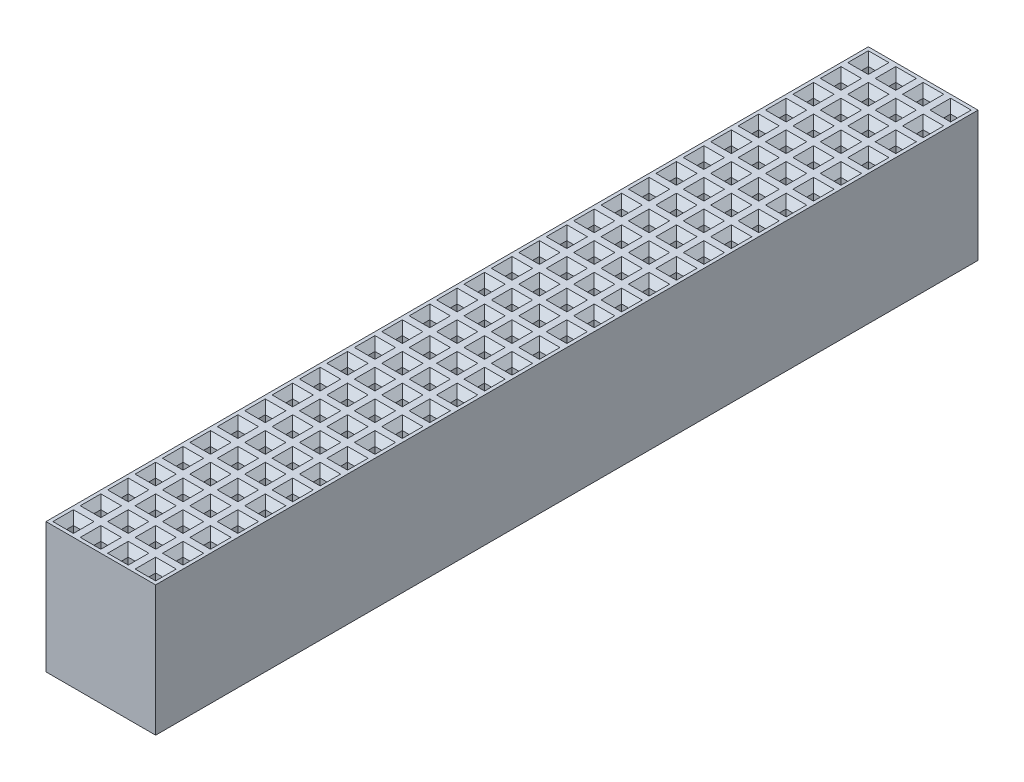
SolidWorks part; units mm, degrees
ref_plane "Alzado" through (0, 0, 0) normal (0, 0, 1) x (1, 0, 0)
ref_plane "Planta" through (0, 0, 0) normal (0, 1, 0) x (1, 0, 0)
ref_plane "Vista lateral" through (0, 0, 0) normal (1, 0, 0) x (0, 0, -1)
sketch "Croquis1" plane through (0, 0, 0) normal (0, 1, 0) x (1, 0, 0)
  line L1 (0, 0) -> (8, 0)
  line L2 (0, 0) -> (0, 60)
  line L3 (0, 60) -> (8, 60)
  line L4 (8, 0) -> (8, 60)
  dimension "D1" = 60
  dimension "D2" = 8
extrude "Extruir1" add sketch "Croquis1" along normal blind 9.5
sketch "Croquis2" plane through (0, 9.5, 0) normal (0, 1, 0) x (1, 0, 0)
  line L0 (0, 0) -> (8, 0) construction
  line L1 (6.75, 1.25) -> (7.25, 1.25)
  line L2 (6.75, 1.25) -> (6.75, 0.75)
  line L3 (6.75, 0.75) -> (7.25, 0.75)
  line L4 (7.25, 1.25) -> (7.25, 0.75)
  line L5 (8, 0) -> (8, 60) construction
  line L6 (4.75, 1.25) -> (5.25, 1.25)
  line L7 (4.75, 1.25) -> (4.75, 0.75)
  line L8 (4.75, 0.75) -> (5.25, 0.75)
  line L9 (5.25, 1.25) -> (5.25, 0.75)
  line L10 (2.75, 1.25) -> (3.25, 1.25)
  line L11 (2.75, 1.25) -> (2.75, 0.75)
  line L12 (2.75, 0.75) -> (3.25, 0.75)
  line L13 (3.25, 1.25) -> (3.25, 0.75)
  line L14 (0.75, 1.25) -> (1.25, 1.25)
  line L15 (0.75, 1.25) -> (0.75, 0.75)
  line L16 (0.75, 0.75) -> (1.25, 0.75)
  line L17 (1.25, 1.25) -> (1.25, 0.75)
  line L18 (6.75, 3.25) -> (7.25, 3.25)
  line L19 (6.75, 3.25) -> (6.75, 2.75)
  line L20 (6.75, 2.75) -> (7.25, 2.75)
  line L21 (7.25, 3.25) -> (7.25, 2.75)
  line L22 (4.75, 3.25) -> (5.25, 3.25)
  line L23 (4.75, 3.25) -> (4.75, 2.75)
  line L24 (4.75, 2.75) -> (5.25, 2.75)
  line L25 (5.25, 3.25) -> (5.25, 2.75)
  line L26 (2.75, 3.25) -> (3.25, 3.25)
  line L27 (2.75, 3.25) -> (2.75, 2.75)
  line L28 (2.75, 2.75) -> (3.25, 2.75)
  line L29 (3.25, 3.25) -> (3.25, 2.75)
  line L30 (0.75, 3.25) -> (1.25, 3.25)
  line L31 (0.75, 3.25) -> (0.75, 2.75)
  line L32 (0.75, 2.75) -> (1.25, 2.75)
  line L33 (1.25, 3.25) -> (1.25, 2.75)
  line L34 (6.75, 5.25) -> (7.25, 5.25)
  line L35 (6.75, 5.25) -> (6.75, 4.75)
  line L36 (6.75, 4.75) -> (7.25, 4.75)
  line L37 (7.25, 5.25) -> (7.25, 4.75)
  line L38 (4.75, 5.25) -> (5.25, 5.25)
  line L39 (4.75, 5.25) -> (4.75, 4.75)
  line L40 (4.75, 4.75) -> (5.25, 4.75)
  line L41 (5.25, 5.25) -> (5.25, 4.75)
  line L42 (2.75, 5.25) -> (3.25, 5.25)
  line L43 (2.75, 5.25) -> (2.75, 4.75)
  line L44 (2.75, 4.75) -> (3.25, 4.75)
  line L45 (3.25, 5.25) -> (3.25, 4.75)
  line L46 (0.75, 5.25) -> (1.25, 5.25)
  line L47 (0.75, 5.25) -> (0.75, 4.75)
  line L48 (0.75, 4.75) -> (1.25, 4.75)
  line L49 (1.25, 5.25) -> (1.25, 4.75)
  line L50 (6.75, 7.25) -> (7.25, 7.25)
  line L51 (6.75, 7.25) -> (6.75, 6.75)
  line L52 (6.75, 6.75) -> (7.25, 6.75)
  line L53 (7.25, 7.25) -> (7.25, 6.75)
  line L54 (4.75, 7.25) -> (5.25, 7.25)
  line L55 (4.75, 7.25) -> (4.75, 6.75)
  line L56 (4.75, 6.75) -> (5.25, 6.75)
  line L57 (5.25, 7.25) -> (5.25, 6.75)
  line L58 (2.75, 7.25) -> (3.25, 7.25)
  line L59 (2.75, 7.25) -> (2.75, 6.75)
  line L60 (2.75, 6.75) -> (3.25, 6.75)
  line L61 (3.25, 7.25) -> (3.25, 6.75)
  line L62 (0.75, 7.25) -> (1.25, 7.25)
  line L63 (0.75, 7.25) -> (0.75, 6.75)
  line L64 (0.75, 6.75) -> (1.25, 6.75)
  line L65 (1.25, 7.25) -> (1.25, 6.75)
  line L66 (6.75, 9.25) -> (7.25, 9.25)
  line L67 (6.75, 9.25) -> (6.75, 8.75)
  line L68 (6.75, 8.75) -> (7.25, 8.75)
  line L69 (7.25, 9.25) -> (7.25, 8.75)
  line L70 (4.75, 9.25) -> (5.25, 9.25)
  line L71 (4.75, 9.25) -> (4.75, 8.75)
  line L72 (4.75, 8.75) -> (5.25, 8.75)
  line L73 (5.25, 9.25) -> (5.25, 8.75)
  line L74 (2.75, 9.25) -> (3.25, 9.25)
  line L75 (2.75, 9.25) -> (2.75, 8.75)
  line L76 (2.75, 8.75) -> (3.25, 8.75)
  line L77 (3.25, 9.25) -> (3.25, 8.75)
  line L78 (0.75, 9.25) -> (1.25, 9.25)
  line L79 (0.75, 9.25) -> (0.75, 8.75)
  line L80 (0.75, 8.75) -> (1.25, 8.75)
  line L81 (1.25, 9.25) -> (1.25, 8.75)
  line L82 (6.75, 11.25) -> (7.25, 11.25)
  line L83 (6.75, 11.25) -> (6.75, 10.75)
  line L84 (6.75, 10.75) -> (7.25, 10.75)
  line L85 (7.25, 11.25) -> (7.25, 10.75)
  line L86 (4.75, 11.25) -> (5.25, 11.25)
  line L87 (4.75, 11.25) -> (4.75, 10.75)
  line L88 (4.75, 10.75) -> (5.25, 10.75)
  line L89 (5.25, 11.25) -> (5.25, 10.75)
  line L90 (2.75, 11.25) -> (3.25, 11.25)
  line L91 (2.75, 11.25) -> (2.75, 10.75)
  line L92 (2.75, 10.75) -> (3.25, 10.75)
  line L93 (3.25, 11.25) -> (3.25, 10.75)
  line L94 (0.75, 11.25) -> (1.25, 11.25)
  line L95 (0.75, 11.25) -> (0.75, 10.75)
  line L96 (0.75, 10.75) -> (1.25, 10.75)
  line L97 (1.25, 11.25) -> (1.25, 10.75)
  line L98 (6.75, 13.25) -> (7.25, 13.25)
  line L99 (6.75, 13.25) -> (6.75, 12.75)
  line L100 (6.75, 12.75) -> (7.25, 12.75)
  line L101 (7.25, 13.25) -> (7.25, 12.75)
  line L102 (4.75, 13.25) -> (5.25, 13.25)
  line L103 (4.75, 13.25) -> (4.75, 12.75)
  line L104 (4.75, 12.75) -> (5.25, 12.75)
  line L105 (5.25, 13.25) -> (5.25, 12.75)
  line L106 (2.75, 13.25) -> (3.25, 13.25)
  line L107 (2.75, 13.25) -> (2.75, 12.75)
  line L108 (2.75, 12.75) -> (3.25, 12.75)
  line L109 (3.25, 13.25) -> (3.25, 12.75)
  line L110 (0.75, 13.25) -> (1.25, 13.25)
  line L111 (0.75, 13.25) -> (0.75, 12.75)
  line L112 (0.75, 12.75) -> (1.25, 12.75)
  line L113 (1.25, 13.25) -> (1.25, 12.75)
  line L114 (6.75, 15.25) -> (7.25, 15.25)
  line L115 (6.75, 15.25) -> (6.75, 14.75)
  line L116 (6.75, 14.75) -> (7.25, 14.75)
  line L117 (7.25, 15.25) -> (7.25, 14.75)
  line L118 (4.75, 15.25) -> (5.25, 15.25)
  line L119 (4.75, 15.25) -> (4.75, 14.75)
  line L120 (4.75, 14.75) -> (5.25, 14.75)
  line L121 (5.25, 15.25) -> (5.25, 14.75)
  line L122 (2.75, 15.25) -> (3.25, 15.25)
  line L123 (2.75, 15.25) -> (2.75, 14.75)
  line L124 (2.75, 14.75) -> (3.25, 14.75)
  line L125 (3.25, 15.25) -> (3.25, 14.75)
  line L126 (0.75, 15.25) -> (1.25, 15.25)
  line L127 (0.75, 15.25) -> (0.75, 14.75)
  line L128 (0.75, 14.75) -> (1.25, 14.75)
  line L129 (1.25, 15.25) -> (1.25, 14.75)
  line L130 (6.75, 17.25) -> (7.25, 17.25)
  line L131 (6.75, 17.25) -> (6.75, 16.75)
  line L132 (6.75, 16.75) -> (7.25, 16.75)
  line L133 (7.25, 17.25) -> (7.25, 16.75)
  line L134 (4.75, 17.25) -> (5.25, 17.25)
  line L135 (4.75, 17.25) -> (4.75, 16.75)
  line L136 (4.75, 16.75) -> (5.25, 16.75)
  line L137 (5.25, 17.25) -> (5.25, 16.75)
  line L138 (2.75, 17.25) -> (3.25, 17.25)
  line L139 (2.75, 17.25) -> (2.75, 16.75)
  line L140 (2.75, 16.75) -> (3.25, 16.75)
  line L141 (3.25, 17.25) -> (3.25, 16.75)
  line L142 (0.75, 17.25) -> (1.25, 17.25)
  line L143 (0.75, 17.25) -> (0.75, 16.75)
  line L144 (0.75, 16.75) -> (1.25, 16.75)
  line L145 (1.25, 17.25) -> (1.25, 16.75)
  line L146 (6.75, 19.25) -> (7.25, 19.25)
  line L147 (6.75, 19.25) -> (6.75, 18.75)
  line L148 (6.75, 18.75) -> (7.25, 18.75)
  line L149 (7.25, 19.25) -> (7.25, 18.75)
  line L150 (4.75, 19.25) -> (5.25, 19.25)
  line L151 (4.75, 19.25) -> (4.75, 18.75)
  line L152 (4.75, 18.75) -> (5.25, 18.75)
  line L153 (5.25, 19.25) -> (5.25, 18.75)
  line L154 (2.75, 19.25) -> (3.25, 19.25)
  line L155 (2.75, 19.25) -> (2.75, 18.75)
  line L156 (2.75, 18.75) -> (3.25, 18.75)
  line L157 (3.25, 19.25) -> (3.25, 18.75)
  line L158 (0.75, 19.25) -> (1.25, 19.25)
  line L159 (0.75, 19.25) -> (0.75, 18.75)
  line L160 (0.75, 18.75) -> (1.25, 18.75)
  line L161 (1.25, 19.25) -> (1.25, 18.75)
  line L162 (6.75, 21.25) -> (7.25, 21.25)
  line L163 (6.75, 21.25) -> (6.75, 20.75)
  line L164 (6.75, 20.75) -> (7.25, 20.75)
  line L165 (7.25, 21.25) -> (7.25, 20.75)
  line L166 (4.75, 21.25) -> (5.25, 21.25)
  line L167 (4.75, 21.25) -> (4.75, 20.75)
  line L168 (4.75, 20.75) -> (5.25, 20.75)
  line L169 (5.25, 21.25) -> (5.25, 20.75)
  line L170 (2.75, 21.25) -> (3.25, 21.25)
  line L171 (2.75, 21.25) -> (2.75, 20.75)
  line L172 (2.75, 20.75) -> (3.25, 20.75)
  line L173 (3.25, 21.25) -> (3.25, 20.75)
  line L174 (0.75, 21.25) -> (1.25, 21.25)
  line L175 (0.75, 21.25) -> (0.75, 20.75)
  line L176 (0.75, 20.75) -> (1.25, 20.75)
  line L177 (1.25, 21.25) -> (1.25, 20.75)
  line L178 (6.75, 23.25) -> (7.25, 23.25)
  line L179 (6.75, 23.25) -> (6.75, 22.75)
  line L180 (6.75, 22.75) -> (7.25, 22.75)
  line L181 (7.25, 23.25) -> (7.25, 22.75)
  line L182 (4.75, 23.25) -> (5.25, 23.25)
  line L183 (4.75, 23.25) -> (4.75, 22.75)
  line L184 (4.75, 22.75) -> (5.25, 22.75)
  line L185 (5.25, 23.25) -> (5.25, 22.75)
  line L186 (2.75, 23.25) -> (3.25, 23.25)
  line L187 (2.75, 23.25) -> (2.75, 22.75)
  line L188 (2.75, 22.75) -> (3.25, 22.75)
  line L189 (3.25, 23.25) -> (3.25, 22.75)
  line L190 (0.75, 23.25) -> (1.25, 23.25)
  line L191 (0.75, 23.25) -> (0.75, 22.75)
  line L192 (0.75, 22.75) -> (1.25, 22.75)
  line L193 (1.25, 23.25) -> (1.25, 22.75)
  line L194 (6.75, 25.25) -> (7.25, 25.25)
  line L195 (6.75, 25.25) -> (6.75, 24.75)
  line L196 (6.75, 24.75) -> (7.25, 24.75)
  line L197 (7.25, 25.25) -> (7.25, 24.75)
  line L198 (4.75, 25.25) -> (5.25, 25.25)
  line L199 (4.75, 25.25) -> (4.75, 24.75)
  line L200 (4.75, 24.75) -> (5.25, 24.75)
  line L201 (5.25, 25.25) -> (5.25, 24.75)
  line L202 (2.75, 25.25) -> (3.25, 25.25)
  line L203 (2.75, 25.25) -> (2.75, 24.75)
  line L204 (2.75, 24.75) -> (3.25, 24.75)
  line L205 (3.25, 25.25) -> (3.25, 24.75)
  line L206 (0.75, 25.25) -> (1.25, 25.25)
  line L207 (0.75, 25.25) -> (0.75, 24.75)
  line L208 (0.75, 24.75) -> (1.25, 24.75)
  line L209 (1.25, 25.25) -> (1.25, 24.75)
  line L210 (6.75, 27.25) -> (7.25, 27.25)
  line L211 (6.75, 27.25) -> (6.75, 26.75)
  line L212 (6.75, 26.75) -> (7.25, 26.75)
  line L213 (7.25, 27.25) -> (7.25, 26.75)
  line L214 (4.75, 27.25) -> (5.25, 27.25)
  line L215 (4.75, 27.25) -> (4.75, 26.75)
  line L216 (4.75, 26.75) -> (5.25, 26.75)
  line L217 (5.25, 27.25) -> (5.25, 26.75)
  line L218 (2.75, 27.25) -> (3.25, 27.25)
  line L219 (2.75, 27.25) -> (2.75, 26.75)
  line L220 (2.75, 26.75) -> (3.25, 26.75)
  line L221 (3.25, 27.25) -> (3.25, 26.75)
  line L222 (0.75, 27.25) -> (1.25, 27.25)
  line L223 (0.75, 27.25) -> (0.75, 26.75)
  line L224 (0.75, 26.75) -> (1.25, 26.75)
  line L225 (1.25, 27.25) -> (1.25, 26.75)
  line L226 (6.75, 29.25) -> (7.25, 29.25)
  line L227 (6.75, 29.25) -> (6.75, 28.75)
  line L228 (6.75, 28.75) -> (7.25, 28.75)
  line L229 (7.25, 29.25) -> (7.25, 28.75)
  line L230 (4.75, 29.25) -> (5.25, 29.25)
  line L231 (4.75, 29.25) -> (4.75, 28.75)
  line L232 (4.75, 28.75) -> (5.25, 28.75)
  line L233 (5.25, 29.25) -> (5.25, 28.75)
  line L234 (2.75, 29.25) -> (3.25, 29.25)
  line L235 (2.75, 29.25) -> (2.75, 28.75)
  line L236 (2.75, 28.75) -> (3.25, 28.75)
  line L237 (3.25, 29.25) -> (3.25, 28.75)
  line L238 (0.75, 29.25) -> (1.25, 29.25)
  line L239 (0.75, 29.25) -> (0.75, 28.75)
  line L240 (0.75, 28.75) -> (1.25, 28.75)
  line L241 (1.25, 29.25) -> (1.25, 28.75)
  line L242 (6.75, 31.25) -> (7.25, 31.25)
  line L243 (6.75, 31.25) -> (6.75, 30.75)
  line L244 (6.75, 30.75) -> (7.25, 30.75)
  line L245 (7.25, 31.25) -> (7.25, 30.75)
  line L246 (4.75, 31.25) -> (5.25, 31.25)
  line L247 (4.75, 31.25) -> (4.75, 30.75)
  line L248 (4.75, 30.75) -> (5.25, 30.75)
  line L249 (5.25, 31.25) -> (5.25, 30.75)
  line L250 (2.75, 31.25) -> (3.25, 31.25)
  line L251 (2.75, 31.25) -> (2.75, 30.75)
  line L252 (2.75, 30.75) -> (3.25, 30.75)
  line L253 (3.25, 31.25) -> (3.25, 30.75)
  line L254 (0.75, 31.25) -> (1.25, 31.25)
  line L255 (0.75, 31.25) -> (0.75, 30.75)
  line L256 (0.75, 30.75) -> (1.25, 30.75)
  line L257 (1.25, 31.25) -> (1.25, 30.75)
  line L258 (6.75, 33.25) -> (7.25, 33.25)
  line L259 (6.75, 33.25) -> (6.75, 32.75)
  line L260 (6.75, 32.75) -> (7.25, 32.75)
  line L261 (7.25, 33.25) -> (7.25, 32.75)
  line L262 (4.75, 33.25) -> (5.25, 33.25)
  line L263 (4.75, 33.25) -> (4.75, 32.75)
  line L264 (4.75, 32.75) -> (5.25, 32.75)
  line L265 (5.25, 33.25) -> (5.25, 32.75)
  line L266 (2.75, 33.25) -> (3.25, 33.25)
  line L267 (2.75, 33.25) -> (2.75, 32.75)
  line L268 (2.75, 32.75) -> (3.25, 32.75)
  line L269 (3.25, 33.25) -> (3.25, 32.75)
  line L270 (0.75, 33.25) -> (1.25, 33.25)
  line L271 (0.75, 33.25) -> (0.75, 32.75)
  line L272 (0.75, 32.75) -> (1.25, 32.75)
  line L273 (1.25, 33.25) -> (1.25, 32.75)
  line L274 (6.75, 35.25) -> (7.25, 35.25)
  line L275 (6.75, 35.25) -> (6.75, 34.75)
  line L276 (6.75, 34.75) -> (7.25, 34.75)
  line L277 (7.25, 35.25) -> (7.25, 34.75)
  line L278 (4.75, 35.25) -> (5.25, 35.25)
  line L279 (4.75, 35.25) -> (4.75, 34.75)
  line L280 (4.75, 34.75) -> (5.25, 34.75)
  line L281 (5.25, 35.25) -> (5.25, 34.75)
  line L282 (2.75, 35.25) -> (3.25, 35.25)
  line L283 (2.75, 35.25) -> (2.75, 34.75)
  line L284 (2.75, 34.75) -> (3.25, 34.75)
  line L285 (3.25, 35.25) -> (3.25, 34.75)
  line L286 (0.75, 35.25) -> (1.25, 35.25)
  line L287 (0.75, 35.25) -> (0.75, 34.75)
  line L288 (0.75, 34.75) -> (1.25, 34.75)
  line L289 (1.25, 35.25) -> (1.25, 34.75)
  line L290 (6.75, 37.25) -> (7.25, 37.25)
  line L291 (6.75, 37.25) -> (6.75, 36.75)
  line L292 (6.75, 36.75) -> (7.25, 36.75)
  line L293 (7.25, 37.25) -> (7.25, 36.75)
  line L294 (4.75, 37.25) -> (5.25, 37.25)
  line L295 (4.75, 37.25) -> (4.75, 36.75)
  line L296 (4.75, 36.75) -> (5.25, 36.75)
  line L297 (5.25, 37.25) -> (5.25, 36.75)
  line L298 (2.75, 37.25) -> (3.25, 37.25)
  line L299 (2.75, 37.25) -> (2.75, 36.75)
  line L300 (2.75, 36.75) -> (3.25, 36.75)
  line L301 (3.25, 37.25) -> (3.25, 36.75)
  line L302 (0.75, 37.25) -> (1.25, 37.25)
  line L303 (0.75, 37.25) -> (0.75, 36.75)
  line L304 (0.75, 36.75) -> (1.25, 36.75)
  line L305 (1.25, 37.25) -> (1.25, 36.75)
  line L306 (6.75, 39.25) -> (7.25, 39.25)
  line L307 (6.75, 39.25) -> (6.75, 38.75)
  line L308 (6.75, 38.75) -> (7.25, 38.75)
  line L309 (7.25, 39.25) -> (7.25, 38.75)
  line L310 (4.75, 39.25) -> (5.25, 39.25)
  line L311 (4.75, 39.25) -> (4.75, 38.75)
  line L312 (4.75, 38.75) -> (5.25, 38.75)
  line L313 (5.25, 39.25) -> (5.25, 38.75)
  line L314 (2.75, 39.25) -> (3.25, 39.25)
  line L315 (2.75, 39.25) -> (2.75, 38.75)
  line L316 (2.75, 38.75) -> (3.25, 38.75)
  line L317 (3.25, 39.25) -> (3.25, 38.75)
  line L318 (0.75, 39.25) -> (1.25, 39.25)
  line L319 (0.75, 39.25) -> (0.75, 38.75)
  line L320 (0.75, 38.75) -> (1.25, 38.75)
  line L321 (1.25, 39.25) -> (1.25, 38.75)
  line L322 (6.75, 41.25) -> (7.25, 41.25)
  line L323 (6.75, 41.25) -> (6.75, 40.75)
  line L324 (6.75, 40.75) -> (7.25, 40.75)
  line L325 (7.25, 41.25) -> (7.25, 40.75)
  line L326 (4.75, 41.25) -> (5.25, 41.25)
  line L327 (4.75, 41.25) -> (4.75, 40.75)
  line L328 (4.75, 40.75) -> (5.25, 40.75)
  line L329 (5.25, 41.25) -> (5.25, 40.75)
  line L330 (2.75, 41.25) -> (3.25, 41.25)
  line L331 (2.75, 41.25) -> (2.75, 40.75)
  line L332 (2.75, 40.75) -> (3.25, 40.75)
  line L333 (3.25, 41.25) -> (3.25, 40.75)
  line L334 (0.75, 41.25) -> (1.25, 41.25)
  line L335 (0.75, 41.25) -> (0.75, 40.75)
  line L336 (0.75, 40.75) -> (1.25, 40.75)
  line L337 (1.25, 41.25) -> (1.25, 40.75)
  line L338 (6.75, 43.25) -> (7.25, 43.25)
  line L339 (6.75, 43.25) -> (6.75, 42.75)
  line L340 (6.75, 42.75) -> (7.25, 42.75)
  line L341 (7.25, 43.25) -> (7.25, 42.75)
  line L342 (4.75, 43.25) -> (5.25, 43.25)
  line L343 (4.75, 43.25) -> (4.75, 42.75)
  line L344 (4.75, 42.75) -> (5.25, 42.75)
  line L345 (5.25, 43.25) -> (5.25, 42.75)
  line L346 (2.75, 43.25) -> (3.25, 43.25)
  line L347 (2.75, 43.25) -> (2.75, 42.75)
  line L348 (2.75, 42.75) -> (3.25, 42.75)
  line L349 (3.25, 43.25) -> (3.25, 42.75)
  line L350 (0.75, 43.25) -> (1.25, 43.25)
  line L351 (0.75, 43.25) -> (0.75, 42.75)
  line L352 (0.75, 42.75) -> (1.25, 42.75)
  line L353 (1.25, 43.25) -> (1.25, 42.75)
  line L354 (6.75, 45.25) -> (7.25, 45.25)
  line L355 (6.75, 45.25) -> (6.75, 44.75)
  line L356 (6.75, 44.75) -> (7.25, 44.75)
  line L357 (7.25, 45.25) -> (7.25, 44.75)
  line L358 (4.75, 45.25) -> (5.25, 45.25)
  line L359 (4.75, 45.25) -> (4.75, 44.75)
  line L360 (4.75, 44.75) -> (5.25, 44.75)
  line L361 (5.25, 45.25) -> (5.25, 44.75)
  line L362 (2.75, 45.25) -> (3.25, 45.25)
  line L363 (2.75, 45.25) -> (2.75, 44.75)
  line L364 (2.75, 44.75) -> (3.25, 44.75)
  line L365 (3.25, 45.25) -> (3.25, 44.75)
  line L366 (0.75, 45.25) -> (1.25, 45.25)
  line L367 (0.75, 45.25) -> (0.75, 44.75)
  line L368 (0.75, 44.75) -> (1.25, 44.75)
  line L369 (1.25, 45.25) -> (1.25, 44.75)
  line L370 (6.75, 47.25) -> (7.25, 47.25)
  line L371 (6.75, 47.25) -> (6.75, 46.75)
  line L372 (6.75, 46.75) -> (7.25, 46.75)
  line L373 (7.25, 47.25) -> (7.25, 46.75)
  line L374 (4.75, 47.25) -> (5.25, 47.25)
  line L375 (4.75, 47.25) -> (4.75, 46.75)
  line L376 (4.75, 46.75) -> (5.25, 46.75)
  line L377 (5.25, 47.25) -> (5.25, 46.75)
  line L378 (2.75, 47.25) -> (3.25, 47.25)
  line L379 (2.75, 47.25) -> (2.75, 46.75)
  line L380 (2.75, 46.75) -> (3.25, 46.75)
  line L381 (3.25, 47.25) -> (3.25, 46.75)
  line L382 (0.75, 47.25) -> (1.25, 47.25)
  line L383 (0.75, 47.25) -> (0.75, 46.75)
  line L384 (0.75, 46.75) -> (1.25, 46.75)
  line L385 (1.25, 47.25) -> (1.25, 46.75)
  line L386 (6.75, 49.25) -> (7.25, 49.25)
  line L387 (6.75, 49.25) -> (6.75, 48.75)
  line L388 (6.75, 48.75) -> (7.25, 48.75)
  line L389 (7.25, 49.25) -> (7.25, 48.75)
  line L390 (4.75, 49.25) -> (5.25, 49.25)
  line L391 (4.75, 49.25) -> (4.75, 48.75)
  line L392 (4.75, 48.75) -> (5.25, 48.75)
  line L393 (5.25, 49.25) -> (5.25, 48.75)
  line L394 (2.75, 49.25) -> (3.25, 49.25)
  line L395 (2.75, 49.25) -> (2.75, 48.75)
  line L396 (2.75, 48.75) -> (3.25, 48.75)
  line L397 (3.25, 49.25) -> (3.25, 48.75)
  line L398 (0.75, 49.25) -> (1.25, 49.25)
  line L399 (0.75, 49.25) -> (0.75, 48.75)
  line L400 (0.75, 48.75) -> (1.25, 48.75)
  line L401 (1.25, 49.25) -> (1.25, 48.75)
  line L402 (6.75, 51.25) -> (7.25, 51.25)
  line L403 (6.75, 51.25) -> (6.75, 50.75)
  line L404 (6.75, 50.75) -> (7.25, 50.75)
  line L405 (7.25, 51.25) -> (7.25, 50.75)
  line L406 (4.75, 51.25) -> (5.25, 51.25)
  line L407 (4.75, 51.25) -> (4.75, 50.75)
  line L408 (4.75, 50.75) -> (5.25, 50.75)
  line L409 (5.25, 51.25) -> (5.25, 50.75)
  line L410 (2.75, 51.25) -> (3.25, 51.25)
  line L411 (2.75, 51.25) -> (2.75, 50.75)
  line L412 (2.75, 50.75) -> (3.25, 50.75)
  line L413 (3.25, 51.25) -> (3.25, 50.75)
  line L414 (0.75, 51.25) -> (1.25, 51.25)
  line L415 (0.75, 51.25) -> (0.75, 50.75)
  line L416 (0.75, 50.75) -> (1.25, 50.75)
  line L417 (1.25, 51.25) -> (1.25, 50.75)
  line L418 (6.75, 53.25) -> (7.25, 53.25)
  line L419 (6.75, 53.25) -> (6.75, 52.75)
  line L420 (6.75, 52.75) -> (7.25, 52.75)
  line L421 (7.25, 53.25) -> (7.25, 52.75)
  line L422 (4.75, 53.25) -> (5.25, 53.25)
  line L423 (4.75, 53.25) -> (4.75, 52.75)
  line L424 (4.75, 52.75) -> (5.25, 52.75)
  line L425 (5.25, 53.25) -> (5.25, 52.75)
  line L426 (2.75, 53.25) -> (3.25, 53.25)
  line L427 (2.75, 53.25) -> (2.75, 52.75)
  line L428 (2.75, 52.75) -> (3.25, 52.75)
  line L429 (3.25, 53.25) -> (3.25, 52.75)
  line L430 (0.75, 53.25) -> (1.25, 53.25)
  line L431 (0.75, 53.25) -> (0.75, 52.75)
  line L432 (0.75, 52.75) -> (1.25, 52.75)
  line L433 (1.25, 53.25) -> (1.25, 52.75)
  line L434 (6.75, 55.25) -> (7.25, 55.25)
  line L435 (6.75, 55.25) -> (6.75, 54.75)
  line L436 (6.75, 54.75) -> (7.25, 54.75)
  line L437 (7.25, 55.25) -> (7.25, 54.75)
  line L438 (4.75, 55.25) -> (5.25, 55.25)
  line L439 (4.75, 55.25) -> (4.75, 54.75)
  line L440 (4.75, 54.75) -> (5.25, 54.75)
  line L441 (5.25, 55.25) -> (5.25, 54.75)
  line L442 (2.75, 55.25) -> (3.25, 55.25)
  line L443 (2.75, 55.25) -> (2.75, 54.75)
  line L444 (2.75, 54.75) -> (3.25, 54.75)
  line L445 (3.25, 55.25) -> (3.25, 54.75)
  line L446 (0.75, 55.25) -> (1.25, 55.25)
  line L447 (0.75, 55.25) -> (0.75, 54.75)
  line L448 (0.75, 54.75) -> (1.25, 54.75)
  line L449 (1.25, 55.25) -> (1.25, 54.75)
  line L450 (6.75, 57.25) -> (7.25, 57.25)
  line L451 (6.75, 57.25) -> (6.75, 56.75)
  line L452 (6.75, 56.75) -> (7.25, 56.75)
  line L453 (7.25, 57.25) -> (7.25, 56.75)
  line L454 (4.75, 57.25) -> (5.25, 57.25)
  line L455 (4.75, 57.25) -> (4.75, 56.75)
  line L456 (4.75, 56.75) -> (5.25, 56.75)
  line L457 (5.25, 57.25) -> (5.25, 56.75)
  line L458 (2.75, 57.25) -> (3.25, 57.25)
  line L459 (2.75, 57.25) -> (2.75, 56.75)
  line L460 (2.75, 56.75) -> (3.25, 56.75)
  line L461 (3.25, 57.25) -> (3.25, 56.75)
  line L462 (0.75, 57.25) -> (1.25, 57.25)
  line L463 (0.75, 57.25) -> (0.75, 56.75)
  line L464 (0.75, 56.75) -> (1.25, 56.75)
  line L465 (1.25, 57.25) -> (1.25, 56.75)
  line L466 (6.75, 59.25) -> (7.25, 59.25)
  line L467 (6.75, 59.25) -> (6.75, 58.75)
  line L468 (6.75, 58.75) -> (7.25, 58.75)
  line L469 (7.25, 59.25) -> (7.25, 58.75)
  line L470 (4.75, 59.25) -> (5.25, 59.25)
  line L471 (4.75, 59.25) -> (4.75, 58.75)
  line L472 (4.75, 58.75) -> (5.25, 58.75)
  line L473 (5.25, 59.25) -> (5.25, 58.75)
  line L474 (2.75, 59.25) -> (3.25, 59.25)
  line L475 (2.75, 59.25) -> (2.75, 58.75)
  line L476 (2.75, 58.75) -> (3.25, 58.75)
  line L477 (3.25, 59.25) -> (3.25, 58.75)
  line L478 (0.75, 59.25) -> (1.25, 59.25)
  line L479 (0.75, 59.25) -> (0.75, 58.75)
  line L480 (0.75, 58.75) -> (1.25, 58.75)
  line L481 (1.25, 59.25) -> (1.25, 58.75)
  dimension "D1" = 0.5
  dimension "D2" = 0.5
  dimension "D3" = 0.75
  dimension "D4" = 0.75
extrude "Cortar-Extruir1" cut sketch "Croquis2" against normal blind 8.5
chamfer "Chaflán1" distance 0.5 angle 45 112 edges at (1, 9.5, -12.75) (0.75, 9.5, -13) (1, 9.5, -13.25) (1.25, 9.5, -13) (3, 9.5, -12.75) (2.75, 9.5, -13) (3, 9.5, -13.25) (3.25, 9.5, -13) (5, 9.5, -12.75) (4.75, 9.5, -13) (5, 9.5, -13.25) (5.25, 9.5, -13) (7, 9.5, -12.75) (6.75, 9.5, -13) (7, 9.5, -13.25) (7.25, 9.5, -13) (7, 9.5, -10.75) (7.25, 9.5, -11) (7, 9.5, -11.25) (6.75, 9.5, -11) (5, 9.5, -10.75) (5.25, 9.5, -11) (5, 9.5, -11.25) (4.75, 9.5, -11) (3, 9.5, -10.75) (3.25, 9.5, -11) (3, 9.5, -11.25) (2.75, 9.5, -11) (1, 9.5, -10.75) (0.75, 9.5, -11) (1, 9.5, -11.25) (1.25, 9.5, -11) (0.75, 9.5, -9) (1, 9.5, -9.25) (1.25, 9.5, -9) (1, 9.5, -8.75) (1, 9.5, -6.75) (0.75, 9.5, -7) (1, 9.5, -7.25) (1.25, 9.5, -7) (2.75, 9.5, -9) (3, 9.5, -9.25) (3.25, 9.5, -9) (3, 9.5, -8.75) (3, 9.5, -6.75) (3.25, 9.5, -7) (3, 9.5, -7.25) (2.75, 9.5, -7) (0.75, 9.5, -1) (1, 9.5, -0.75) (1.25, 9.5, -1) (1, 9.5, -1.25) (0.75, 9.5, -3) (1, 9.5, -2.75) (1.25, 9.5, -3) (1, 9.5, -3.25) (1, 9.5, -4.75) (0.75, 9.5, -5) (1, 9.5, -5.25) (1.25, 9.5, -5) (2.75, 9.5, -5) (3, 9.5, -5.25) (3.25, 9.5, -5) (3, 9.5, -4.75) (3, 9.5, -2.75) (3.25, 9.5, -3) (3, 9.5, -3.25) (2.75, 9.5, -3) (2.75, 9.5, -1) (3, 9.5, -1.25) (3.25, 9.5, -1) (3, 9.5, -0.75) (5, 9.5, -0.75) (5.25, 9.5, -1) (5, 9.5, -1.25) (4.75, 9.5, -1) (5, 9.5, -2.75) (4.75, 9.5, -3) (5.25, 9.5, -3) (5, 9.5, -3.25) (5, 9.5, -4.75) (5.25, 9.5, -5) (5, 9.5, -5.25) (4.75, 9.5, -5) (5, 9.5, -6.75) (4.75, 9.5, -7) (5.25, 9.5, -7) (5, 9.5, -7.25) (5, 9.5, -8.75) (5.25, 9.5, -9) (4.75, 9.5, -9) (5, 9.5, -9.25) (7, 9.5, -9.25) (7.25, 9.5, -9) (7, 9.5, -8.75) (6.75, 9.5, -9) (6.75, 9.5, -7) (7, 9.5, -7.25) (7.25, 9.5, -7) (7, 9.5, -6.75) (6.75, 9.5, -5) (7, 9.5, -5.25) (7, 9.5, -4.75) (7.25, 9.5, -5) (7, 9.5, -2.75) (7.25, 9.5, -3) (7, 9.5, -3.25) (6.75, 9.5, -3) (6.75, 9.5, -1) (7, 9.5, -1.25) (7.25, 9.5, -1) (7, 9.5, -0.75)
chamfer "Chaflán3" distance 0.5 angle 45 128 edges at (1, 9.5, -28.75) (0.75, 9.5, -29) (1, 9.5, -29.25) (1.25, 9.5, -29) (3, 9.5, -28.75) (2.75, 9.5, -29) (3, 9.5, -29.25) (3.25, 9.5, -29) (5, 9.5, -28.75) (4.75, 9.5, -29) (5, 9.5, -29.25) (5.25, 9.5, -29) (6.75, 9.5, -29) (7, 9.5, -28.75) (7.25, 9.5, -29) (7, 9.5, -29.25) (7, 9.5, -26.75) (7.25, 9.5, -27) (7, 9.5, -27.25) (6.75, 9.5, -27) (5, 9.5, -26.75) (4.75, 9.5, -27) (5, 9.5, -27.25) (5.25, 9.5, -27) (3.25, 9.5, -27) (3, 9.5, -26.75) (2.75, 9.5, -27) (3, 9.5, -27.25) (1.25, 9.5, -27) (1, 9.5, -26.75) (0.75, 9.5, -27) (1, 9.5, -27.25) (0.75, 9.5, -25) (1, 9.5, -24.75) (1.25, 9.5, -25) (1, 9.5, -25.25) (3, 9.5, -24.75) (2.75, 9.5, -25) (3, 9.5, -25.25) (3.25, 9.5, -25) (5, 9.5, -24.75) (4.75, 9.5, -25) (5, 9.5, -25.25) (5.25, 9.5, -25) (6.75, 9.5, -25) (7, 9.5, -24.75) (7.25, 9.5, -25) (7, 9.5, -25.25) (6.75, 9.5, -23) (7, 9.5, -22.75) (7.25, 9.5, -23) (7, 9.5, -23.25) (5, 9.5, -22.75) (5.25, 9.5, -23) (5, 9.5, -23.25) (4.75, 9.5, -23) (3, 9.5, -22.75) (3.25, 9.5, -23) (3, 9.5, -23.25) (2.75, 9.5, -23) (1, 9.5, -22.75) (1.25, 9.5, -23) (1, 9.5, -23.25) (0.75, 9.5, -23) (1, 9.5, -20.75) (0.75, 9.5, -21) (1, 9.5, -21.25) (1.25, 9.5, -21) (3, 9.5, -20.75) (2.75, 9.5, -21) (3, 9.5, -21.25) (3.25, 9.5, -21) (5, 9.5, -20.75) (4.75, 9.5, -21) (5, 9.5, -21.25) (5.25, 9.5, -21) (7.25, 9.5, -21) (7, 9.5, -21.25) (6.75, 9.5, -21) (7, 9.5, -20.75) (7, 9.5, -18.75) (7.25, 9.5, -19) (7, 9.5, -19.25) (6.75, 9.5, -19) (4.75, 9.5, -19) (5, 9.5, -18.75) (5.25, 9.5, -19) (5, 9.5, -19.25) (3, 9.5, -18.75) (3.25, 9.5, -19) (3, 9.5, -19.25) (2.75, 9.5, -19) (0.75, 9.5, -19) (1, 9.5, -19.25) (1.25, 9.5, -19) (1, 9.5, -18.75) (3, 9.5, -16.75) (3.25, 9.5, -17) (3, 9.5, -17.25) (2.75, 9.5, -17) (1, 9.5, -16.75) (1.25, 9.5, -17) (1, 9.5, -17.25) (0.75, 9.5, -17) (1, 9.5, -15.25) (1.25, 9.5, -15) (1, 9.5, -14.75) (0.75, 9.5, -15) (3, 9.5, -14.75) (2.75, 9.5, -15) (3, 9.5, -15.25) (3.25, 9.5, -15) (4.75, 9.5, -17) (5, 9.5, -17.25) (5.25, 9.5, -17) (5, 9.5, -16.75) (5, 9.5, -14.75) (4.75, 9.5, -15) (5, 9.5, -15.25) (5.25, 9.5, -15) (6.75, 9.5, -15) (7, 9.5, -14.75) (7.25, 9.5, -15) (7, 9.5, -15.25) (6.75, 9.5, -17) (7, 9.5, -17.25) (7, 9.5, -16.75) (7.25, 9.5, -17)
chamfer "Chaflán4" distance 0.5 angle 45 112 edges at (6.75, 9.5, -43) (7, 9.5, -43.25) (7.25, 9.5, -43) (7, 9.5, -42.75) (5, 9.5, -42.75) (5.25, 9.5, -43) (5, 9.5, -43.25) (4.75, 9.5, -43) (2.75, 9.5, -43) (3, 9.5, -42.75) (3.25, 9.5, -43) (3, 9.5, -43.25) (0.75, 9.5, -43) (1, 9.5, -43.25) (1.25, 9.5, -43) (1, 9.5, -42.75) (1, 9.5, -40.75) (0.75, 9.5, -41) (1, 9.5, -41.25) (1.25, 9.5, -41) (2.75, 9.5, -41) (3, 9.5, -40.75) (3.25, 9.5, -41) (3, 9.5, -41.25) (5.25, 9.5, -41) (5, 9.5, -40.75) (4.75, 9.5, -41) (5, 9.5, -41.25) (7, 9.5, -40.75) (6.75, 9.5, -41) (7, 9.5, -41.25) (7.25, 9.5, -41) (6.75, 9.5, -39) (7, 9.5, -38.75) (7.25, 9.5, -39) (7, 9.5, -39.25) (5, 9.5, -38.75) (5.25, 9.5, -39) (5, 9.5, -39.25) (4.75, 9.5, -39) (3, 9.5, -38.75) (3.25, 9.5, -39) (3, 9.5, -39.25) (2.75, 9.5, -39) (1, 9.5, -38.75) (1.25, 9.5, -39) (1, 9.5, -39.25) (0.75, 9.5, -39) (1, 9.5, -36.75) (0.75, 9.5, -37) (1, 9.5, -37.25) (1.25, 9.5, -37) (3, 9.5, -36.75) (2.75, 9.5, -37) (3, 9.5, -37.25) (3.25, 9.5, -37) (5, 9.5, -36.75) (4.75, 9.5, -37) (5, 9.5, -37.25) (5.25, 9.5, -37) (7, 9.5, -36.75) (6.75, 9.5, -37) (7, 9.5, -37.25) (7.25, 9.5, -37) (7, 9.5, -34.75) (6.75, 9.5, -35) (7, 9.5, -35.25) (7.25, 9.5, -35) (5, 9.5, -34.75) (5.25, 9.5, -35) (5, 9.5, -35.25) (4.75, 9.5, -35) (2.75, 9.5, -35) (3, 9.5, -34.75) (3.25, 9.5, -35) (3, 9.5, -35.25) (0.75, 9.5, -35) (1, 9.5, -34.75) (1.25, 9.5, -35) (1, 9.5, -35.25) (1, 9.5, -32.75) (0.75, 9.5, -33) (1, 9.5, -33.25) (1.25, 9.5, -33) (3, 9.5, -32.75) (2.75, 9.5, -33) (3, 9.5, -33.25) (3.25, 9.5, -33) (4.75, 9.5, -33) (5, 9.5, -32.75) (5.25, 9.5, -33) (5, 9.5, -33.25) (7, 9.5, -32.75) (6.75, 9.5, -33) (7, 9.5, -33.25) (7.25, 9.5, -33) (6.75, 9.5, -31) (7, 9.5, -31.25) (7.25, 9.5, -31) (7, 9.5, -30.75) (5, 9.5, -30.75) (5.25, 9.5, -31) (5, 9.5, -31.25) (4.75, 9.5, -31) (1.25, 9.5, -31) (1, 9.5, -30.75) (0.75, 9.5, -31) (1, 9.5, -31.25) (3, 9.5, -30.75) (3.25, 9.5, -31) (2.75, 9.5, -31) (3, 9.5, -31.25)
chamfer "Chaflán5" distance 0.5 angle 45 128 edges at (7, 9.5, -58.75) (6.75, 9.5, -59) (7, 9.5, -59.25) (7.25, 9.5, -59) (4.75, 9.5, -59) (5, 9.5, -58.75) (5.25, 9.5, -59) (5, 9.5, -59.25) (2.75, 9.5, -59) (3, 9.5, -58.75) (3.25, 9.5, -59) (3, 9.5, -59.25) (1, 9.5, -58.75) (1.25, 9.5, -59) (1, 9.5, -59.25) (0.75, 9.5, -59) (1, 9.5, -56.75) (0.75, 9.5, -57) (1, 9.5, -57.25) (1.25, 9.5, -57) (3, 9.5, -56.75) (2.75, 9.5, -57) (3, 9.5, -57.25) (3.25, 9.5, -57) (5, 9.5, -56.75) (4.75, 9.5, -57) (5, 9.5, -57.25) (5.25, 9.5, -57) (7, 9.5, -56.75) (6.75, 9.5, -57) (7, 9.5, -57.25) (7.25, 9.5, -57) (7, 9.5, -54.75) (6.75, 9.5, -55) (7, 9.5, -55.25) (7.25, 9.5, -55) (5, 9.5, -54.75) (4.75, 9.5, -55) (5, 9.5, -55.25) (5.25, 9.5, -55) (3, 9.5, -54.75) (3.25, 9.5, -55) (3, 9.5, -55.25) (2.75, 9.5, -55) (1, 9.5, -54.75) (0.75, 9.5, -55) (1, 9.5, -55.25) (1.25, 9.5, -55) (1, 9.5, -52.75) (0.75, 9.5, -53) (1, 9.5, -53.25) (1.25, 9.5, -53) (3, 9.5, -52.75) (2.75, 9.5, -53) (3, 9.5, -53.25) (3.25, 9.5, -53) (5, 9.5, -52.75) (4.75, 9.5, -53) (5, 9.5, -53.25) (5.25, 9.5, -53) (7, 9.5, -52.75) (6.75, 9.5, -53) (7, 9.5, -53.25) (7.25, 9.5, -53) (6.75, 9.5, -51) (7, 9.5, -50.75) (7.25, 9.5, -51) (7, 9.5, -51.25) (5, 9.5, -50.75) (4.75, 9.5, -51) (5, 9.5, -51.25) (5.25, 9.5, -51) (3, 9.5, -50.75) (3.25, 9.5, -51) (3, 9.5, -51.25) (2.75, 9.5, -51) (1, 9.5, -50.75) (0.75, 9.5, -51) (1, 9.5, -51.25) (1.25, 9.5, -51) (1, 9.5, -48.75) (1.25, 9.5, -49) (0.75, 9.5, -49) (1, 9.5, -49.25) (3, 9.5, -48.75) (2.75, 9.5, -49) (3, 9.5, -49.25) (3.25, 9.5, -49) (4.75, 9.5, -49) (5, 9.5, -49.25) (5.25, 9.5, -49) (5, 9.5, -48.75) (7, 9.5, -48.75) (6.75, 9.5, -49) (7, 9.5, -49.25) (7.25, 9.5, -49) (6.75, 9.5, -47) (7, 9.5, -47.25) (7.25, 9.5, -47) (7, 9.5, -46.75) (5, 9.5, -46.75) (5.25, 9.5, -47) (5, 9.5, -47.25) (4.75, 9.5, -47) (3, 9.5, -46.75) (2.75, 9.5, -47) (3, 9.5, -47.25) (3.25, 9.5, -47) (1, 9.5, -46.75) (1.25, 9.5, -47) (1, 9.5, -47.25) (0.75, 9.5, -47) (1, 9.5, -44.75) (0.75, 9.5, -45) (1, 9.5, -45.25) (1.25, 9.5, -45) (2.75, 9.5, -45) (3, 9.5, -44.75) (3.25, 9.5, -45) (3, 9.5, -45.25) (5, 9.5, -44.75) (4.75, 9.5, -45) (5, 9.5, -45.25) (5.25, 9.5, -45) (6.75, 9.5, -45) (7, 9.5, -44.75) (7.25, 9.5, -45) (7, 9.5, -45.25)
ref_plane "Plano1" through (7, 0, 0) normal (1, 0, 0) x (0, 0, -1)
ref_plane "Plano2" through (0, 0, -1) normal (0, 0, 1) x (1, 0, 0)
